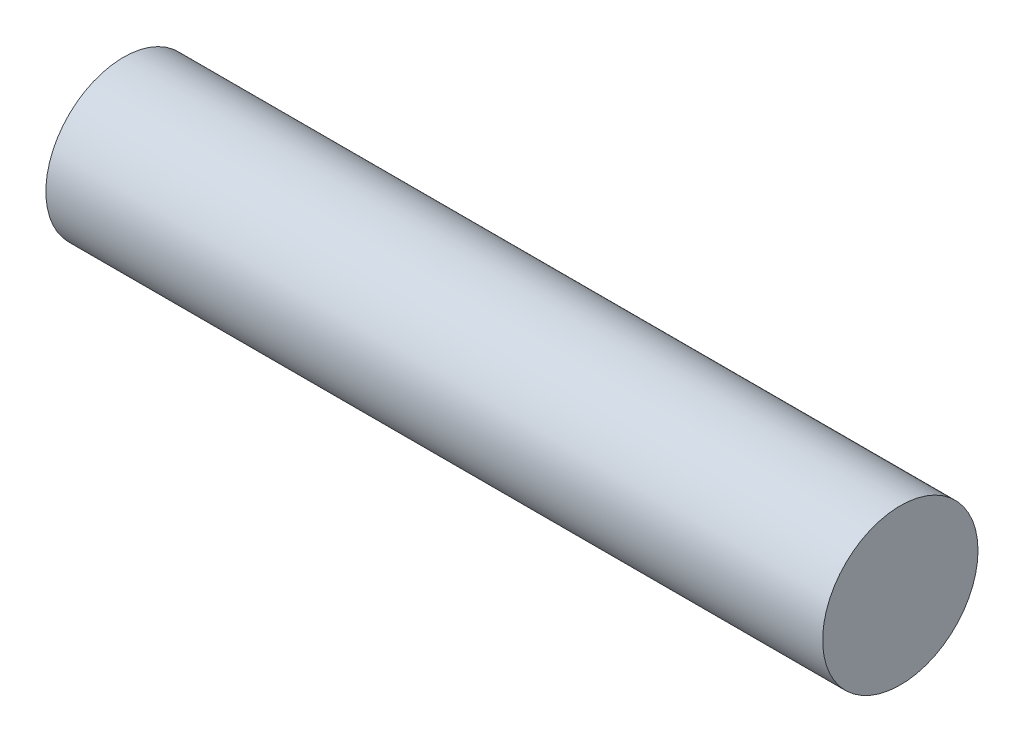
SolidWorks part; units mm, degrees
ref_plane "Front Plane" through (0, 0, 0) normal (0, 0, 1) x (1, 0, 0)
ref_plane "Top Plane" through (0, 0, 0) normal (0, 1, 0) x (1, 0, 0)
ref_plane "Right Plane" through (0, 0, 0) normal (1, 0, 0) x (0, 0, -1)
sketch "Sketch1" plane through (0, 0, 0) normal (1, 0, 0) x (0, 0, -1)
  circle A0 centre (0, 0) radius 1.5875
  dimension "D1" = 3.175
extrude "Boss-Extrude1" add sketch "Sketch1" along normal mid plane 15.875
